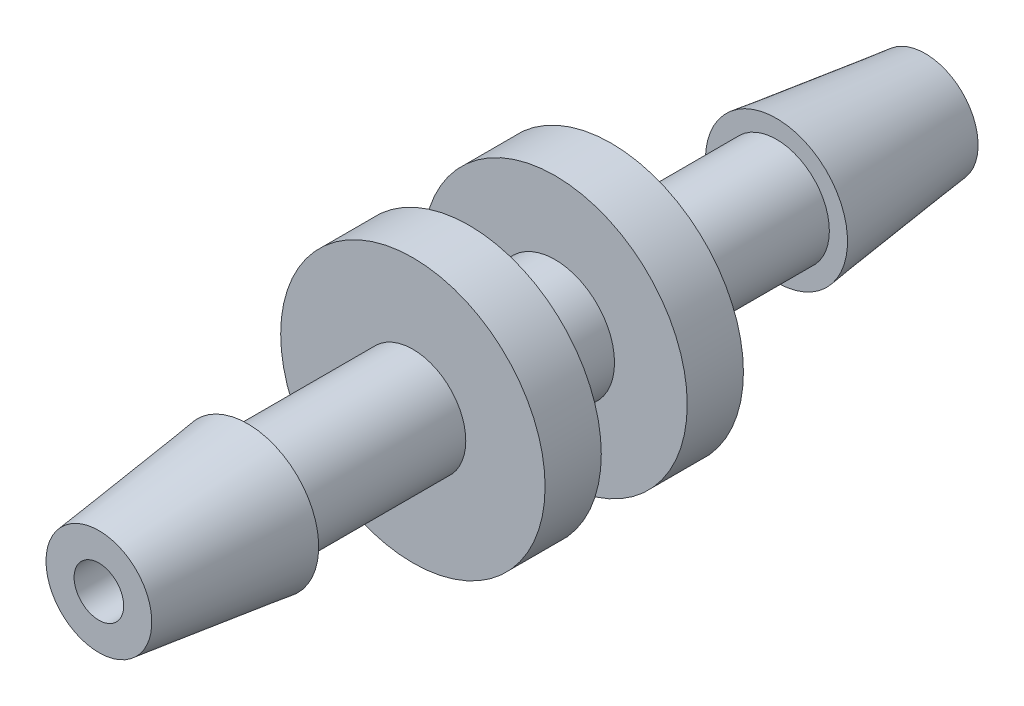
SolidWorks part; units mm, degrees
ref_plane "Front Plane" through (0, 0, 0) normal (0, 0, 1) x (1, 0, 0)
ref_plane "Top Plane" through (0, 0, 0) normal (0, 1, 0) x (1, 0, 0)
ref_plane "Right Plane" through (0, 0, 0) normal (1, 0, 0) x (0, 0, -1)
sketch "Sketch1" plane through (0, 0, 0) normal (0, 0, 1) x (1, 0, 0)
  circle A0 centre (0, 0) radius 1.8
  circle A1 centre (0, 0) radius 0.75
  dimension "D1" = 3.6
  dimension "D2" = 1.5
extrude "Boss-Extrude1" add sketch "Sketch1" along normal blind 1.3
ref_plane "Plane1" through (0, 0, 1.3) normal (0, 0, 1) x (1, 0, 0)
sketch "Sketch2" plane through (0, 0, 1.3) normal (0, 0, 1) x (1, 0, 0)
  circle A0 centre (0, 0) radius 4
  circle A1 centre (0, 0) radius 0.75 construction
  circle A2 centre (0, 0) radius 0.75
  dimension "D1" = 8
extrude "Boss-Extrude2" add sketch "Sketch2" along normal blind 1.7
ref_plane "Plane2" through (0, 0, 3) normal (0, 0, 1) x (1, 0, 0)
sketch "Sketch3" plane through (0, 0, 3) normal (0, 0, 1) x (1, 0, 0)
  circle A0 centre (0, 0) radius 1.6
  circle A1 centre (0, 0) radius 0.75 construction
  circle A2 centre (0, 0) radius 0.75
  dimension "D1" = 3.2
extrude "Boss-Extrude3" add sketch "Sketch3" along normal blind 5
sketch "Sketch5" plane through (0, 0, 0) normal (0, 1, 0) x (1, 0, 0)
  line L0 (0, 0) -> (0, -10.8226) construction
  line L1 (0.75, -8) -> (0.75, -12.5)
  line L2 (-1.6, -8) -> (1.6, -8) construction
  line L3 (0.75, -12.5) -> (1.6, -12.5)
  line L4 (1.6, -12.5) -> (2.15, -8)
  line L5 (0.75, -8) -> (2.15, -8)
  dimension "D1" = 0.75
  dimension "D2" = 1.6
  dimension "D3" = 4.5
  dimension "D4" = 2.15
revolve "Revolve1" add sketch "Sketch5" angle 360 about L0
mirror "Mirror1" about plane through (0, 0, 0) normal (0, 0, 1) of "Boss-Extrude1", "Boss-Extrude2", "Boss-Extrude3", "Revolve1"
